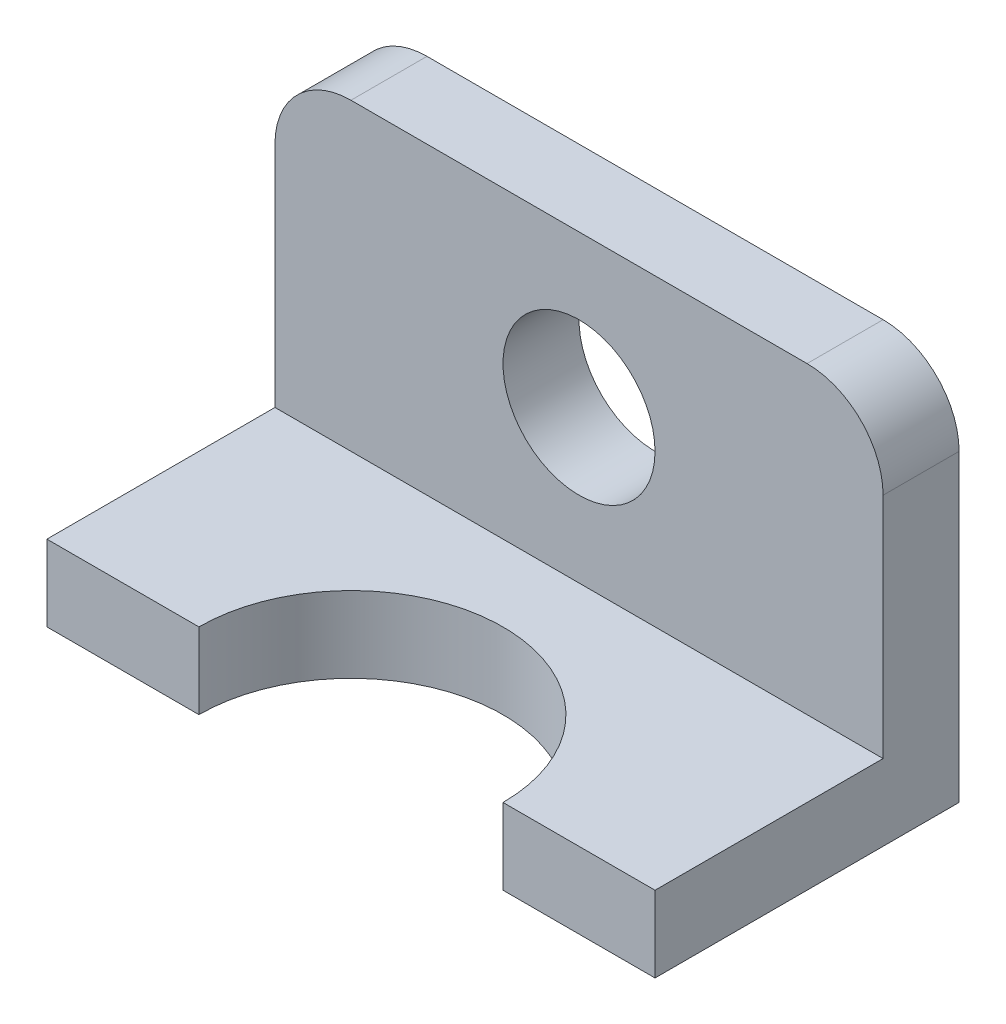
SolidWorks part; units mm, degrees
material "6061 Alloy"
ref_plane "Front Plane" through (0, 0, 0) normal (0, 0, 1) x (1, 0, 0)
ref_plane "Top Plane" through (0, 0, 0) normal (0, 1, 0) x (1, 0, 0)
ref_plane "Right Plane" through (0, 0, 0) normal (1, 0, 0) x (0, 0, -1)
sketch "Sketch1" plane through (0, 0, 0) normal (0, 1, 0) x (1, 0, 0)
  line L0 (-50.8, -50.8) -> (-50.8, 0)
  line L1 (-50.8, 0) -> (50.8, 0)
  line L2 (50.8, 0) -> (50.8, -50.8)
  line L3 (50.8, -50.8) -> (25.4, -50.8)
  line L4 (-50.8, -50.8) -> (-25.4, -50.8)
  arc A0 (-25.4, -50.8) -> (25.4, -50.8) centre (0, -50.8) cw
  point P2 (0, 0)
  point P8 (0, -25.4)
  dimension "D1" = 25.4
  dimension "D2" = 50.8
  dimension "D3" = 101.6
extrude "Boss-Extrude1" add sketch "Sketch1" along normal blind 12.7
sketch "Sketch2" plane through (0, 12.7, 0) normal (0, 1, 0) x (1, 0, 0)
  line L0 (50.8, -50.8) -> (50.8, 0) construction
  line L1 (-50.8, 0) -> (50.8, 0)
  line L2 (-50.8, 0) -> (-50.8, -12.7)
  line L3 (-50.8, -12.7) -> (50.8, -12.7)
  line L4 (50.8, 0) -> (50.8, -12.7)
  dimension "D1" = 12.7
extrude "Boss-Extrude2" add sketch "Sketch2" along normal blind 50.8
sketch "Sketch3" plane through (0, 0, 12.7) normal (0, 0, 1) x (1, 0, 0)
  line L0 (25.4, 12.7) -> (-25.4, 12.7) construction
  circle A0 centre (0, 38.1) radius 12.7
  dimension "D1" = 25.4
  dimension "D2" = 25.4
extrude "Cut-Extrude1" cut sketch "Sketch3" against normal through all
fillet "Fillet2" radius 12.7 2 edges at (50.8, 63.5, 6.35) (-50.8, 63.5, 6.35)
